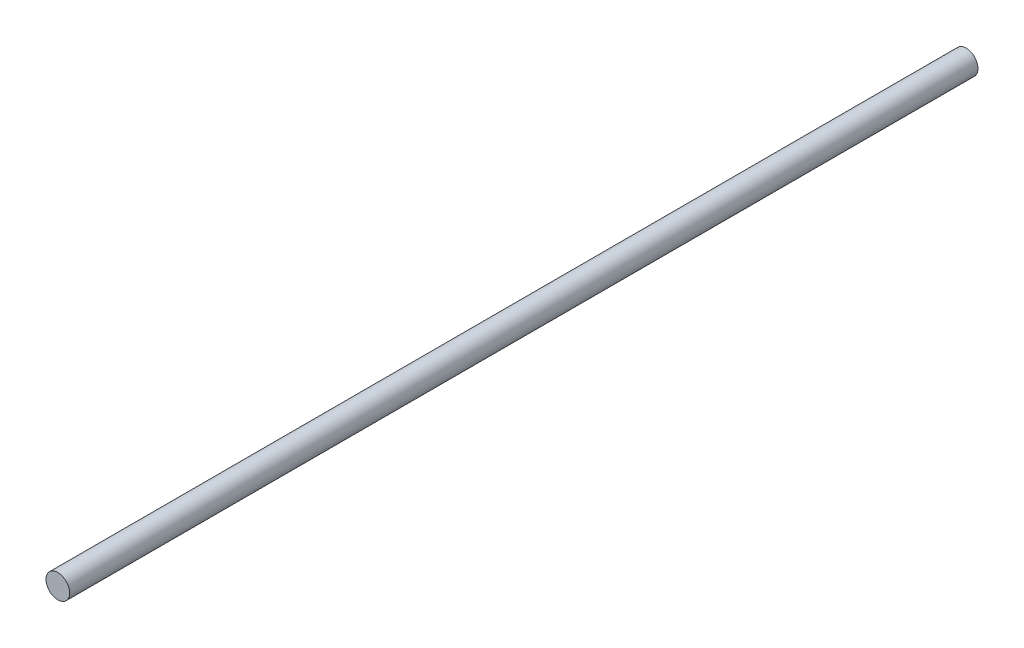
SolidWorks part; units mm, degrees
ref_plane "Front Plane" through (0, 0, 0) normal (0, 0, 1) x (1, 0, 0)
ref_plane "Top Plane" through (0, 0, 0) normal (0, 1, 0) x (1, 0, 0)
ref_plane "Right Plane" through (0, 0, 0) normal (1, 0, 0) x (0, 0, -1)
sketch "Sketch1" plane through (0, 0, 0) normal (0, 0, 1) x (1, 0, 0)
  circle A0 centre (0, 0) radius 3
  dimension "D1" = 6
extrude "Boss-Extrude1" add sketch "Sketch1" along normal blind 230
